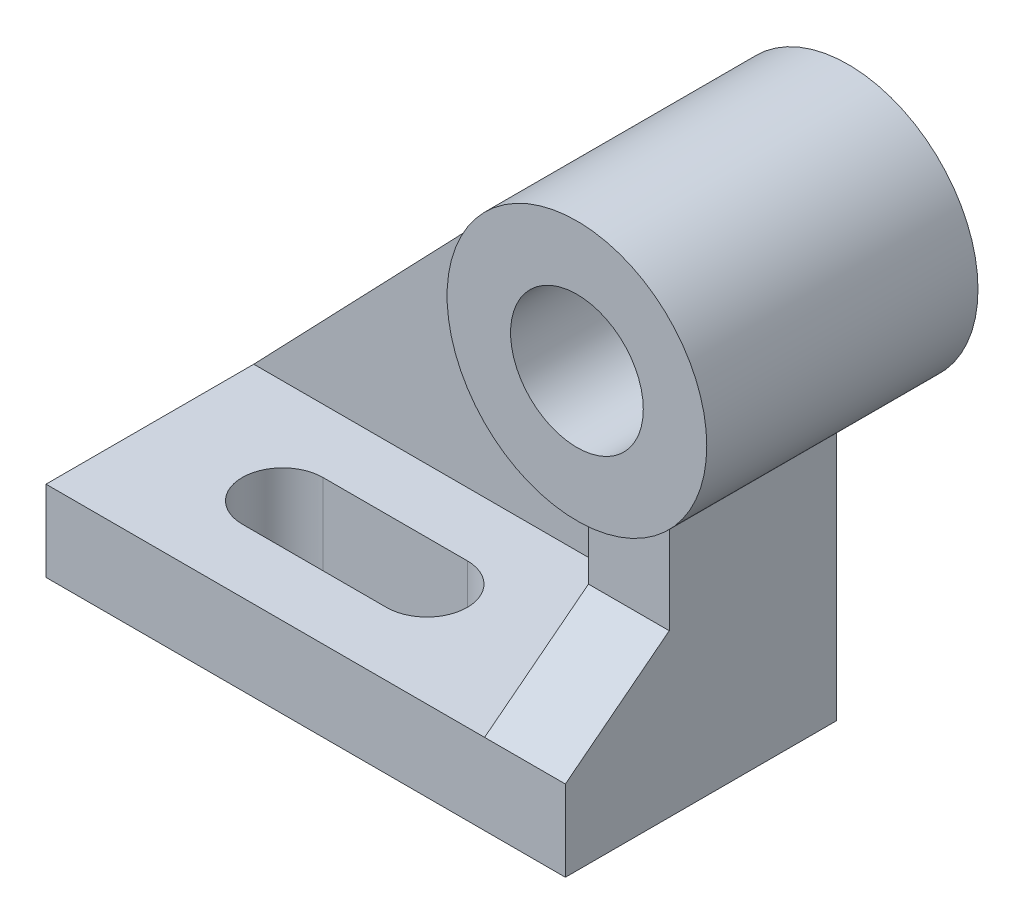
SolidWorks part; units mm, degrees
ref_plane "前视基准面" through (0, 0, 0) normal (0, 0, 1) x (1, 0, 0)
ref_plane "上视基准面" through (0, 0, 0) normal (0, 1, 0) x (1, 0, 0)
ref_plane "右视基准面" through (0, 0, 0) normal (1, 0, 0) x (0, 0, -1)
sketch "草图1" plane through (0, 0, 0) normal (0, 0, 1) x (1, 0, 0)
  circle A0 centre (0, 0) radius 11.5
  circle A1 centre (0, 0) radius 22.5
extrude "凸台-拉伸1" add sketch "草图1" along normal blind 47
ref_plane "基准面1" through (0, 0, 9) normal (0, 0, 1) x (1, 0, 0)
sketch "草图3" plane through (0, 0, 9) normal (0, 0, 1) x (1, 0, 0)
  line L1 (0, -68) -> (7, -68)
  line L2 (7, -68) -> (-83, -68)
  line L3 (7, -68) -> (7, -54)
  line L4 (7, -54) -> (-83, -54)
  line L5 (-83, -68) -> (-83, -54)
extrude "凸台-拉伸2" add sketch "草图3" along normal blind 47 separate body contours L5 L2 L1 L3 L4
sketch "草图4" plane through (0, 0, 9) normal (0, 0, 1) x (1, 0, 0)
  line L0 (-83, -54) -> (-16.2347, 15.5783)
  line L2 (7, -54) -> (-83, -54) construction
  line L3 (-7, -54) -> (-7, -21.3834)
  line L4 (-7, -54) -> (-83, -54)
  circle A0 centre (0, 0) radius 22.5 construction
  arc A1 (-16.2347, 15.5783) -> (-7, -21.3834) centre (0, 0) ccw
extrude "凸台-拉伸3" add sketch "草图4" along normal blind 11
sketch "草图6" plane through (0, 0, 9) normal (0, 0, 1) x (1, 0, 0)
  line L0 (-7, -21.3834) -> (-7, -54)
  line L1 (-7, -54) -> (7, -54)
  line L2 (7, -54) -> (7, -21.3834)
  circle A0 centre (0, 0) radius 22.5 construction
  arc A1 (7, -21.3834) -> (-7, -21.3834) centre (0, 0) cw
extrude "凸台-拉伸10" add sketch "草图6" along normal blind 29 contours L0 L1 L2 A1
ref_plane "基准面2" through (7, 0, 0) normal (1, 0, 0) x (0, 0, -1)
sketch "草图7" plane through (7, 0, 0) normal (1, 0, 0) x (0, 0, -1)
  line L0 (-38, -54) -> (-38, -40)
  line L1 (-38, -54) -> (-38, -21.3834) construction
  line L2 (-38, -40) -> (-56, -54)
  line L3 (-56, -54) -> (-38, -54)
extrude "凸台-拉伸11" add sketch "草图7" against normal blind 14
ref_plane "基准面3" through (0, -168, 0) normal (0, -1, 0) x (-1, 0, 0)
sketch "草图8" plane through (0, -168, 0) normal (0, -1, 0) x (-1, 0, 0)
  line L2 (83, -9) -> (83, -38)
  line L3 (60, -38) -> (35, -38) construction
  line L4 (60, -45) -> (35, -45)
  line L5 (60, -31) -> (35, -31)
  arc A0 (60, -45) -> (60, -31) centre (60, -38) ccw
  arc A1 (35, -31) -> (35, -45) centre (35, -38) ccw
  point P1 (47.5, -38)
extrude "切除-拉伸1" cut sketch "草图8" against normal blind 138 contours L5 A1 L4 A0
